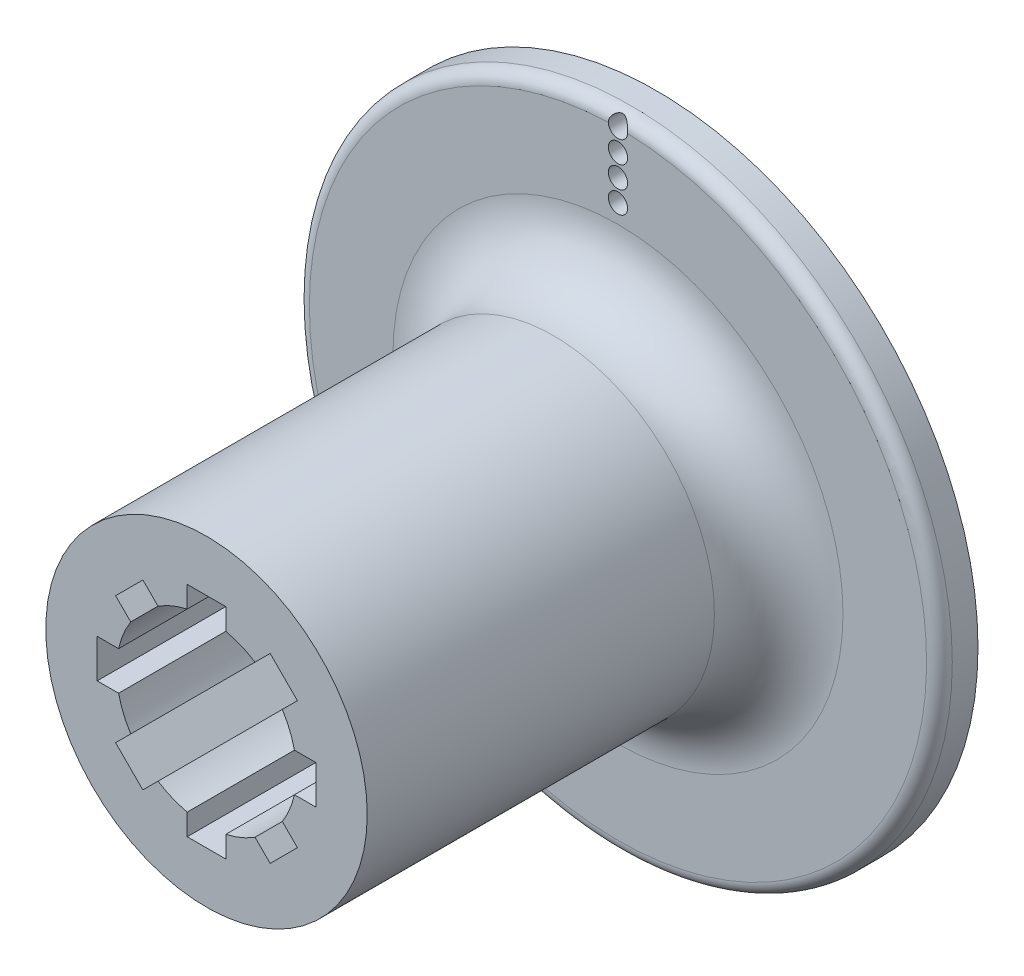
SolidWorks part; units mm, degrees
ref_plane "Front Plane" through (0, 0, 0) normal (0, 0, 1) x (1, 0, 0)
ref_plane "Top Plane" through (0, 0, 0) normal (0, 1, 0) x (1, 0, 0)
ref_plane "Right Plane" through (0, 0, 0) normal (1, 0, 0) x (0, 0, -1)
sketch "Sketch1" plane through (0, 0, 0) normal (0, 0, 1) x (1, 0, 0)
  circle A0 centre (0, 0) radius 28.1
  circle A1 centre (0, 28.1) radius 2.7
  circle A2 centre (24.3353, 14.05) radius 2.7
  circle A3 centre (24.3353, -14.05) radius 2.7
  circle A4 centre (0, -28.1) radius 2.7
  circle A5 centre (-24.3353, -14.05) radius 2.7
  circle A6 centre (-24.3353, 14.05) radius 2.7
  point P18 (0, 0)
  dimension "D1" = 56.2
  dimension "D2" = 5.4
  dimension "D3" = 6
sketch "Sketch3" plane through (0, 0, 0) normal (0, 0, 1) x (1, 0, 0)
  circle A0 centre (0, 0) radius 25
  dimension "D1" = 50
extrude "Boss-Extrude1" add sketch "Sketch3" against normal blind 70
sketch "Sketch4" plane through (0, 0, -70) normal (0, 0, -1) x (-1, 0, 0)
  line L0 (-2.55, 6.6263) -> (-2.55, 9.1)
  line L1 (-2.55, 9.1) -> (2.55, 9.1)
  line L2 (2.55, 9.1) -> (2.55, 6.6263)
  line L3 (0, 0) -> (0, 9.1) construction
  arc A0 (-2.55, 6.6263) -> (2.55, 6.6263) centre (0, 0) ccw
  dimension "D1" = 14.2
  dimension "D2" = 5.1
  dimension "D3" = 16.2
extrude "Cut-Extrude1" cut sketch "Sketch4" against normal blind 32
chamfer "Chamfer1" distance 1 angle 45 4 edges at (-2.55, 7.8631, -70) (0, 9.1, -70) (2.55, 7.8631, -70) (0, -7.1, -70)
sketch "Sketch7" plane through (0, 0, 0) normal (0, 0, 1) x (1, 0, 0)
  line L0 (0, 0) -> (0, 17) construction
  line L1 (-3, 17) -> (3, 17)
  line L2 (-3, 13.6748) -> (-3, 17)
  line L3 (3, 13.6748) -> (3, 17)
  line L4 (7.5482, 11.7909) -> (9.8995, 14.1421)
  line L5 (9.8995, 14.1421) -> (14.1421, 9.8995)
  line L6 (11.7909, 7.5482) -> (14.1421, 9.8995)
  line L7 (13.6748, 3) -> (17, 3)
  line L8 (17, 3) -> (17, -3)
  line L9 (13.6748, -3) -> (17, -3)
  line L10 (11.7909, -7.5482) -> (14.1421, -9.8995)
  line L11 (14.1421, -9.8995) -> (9.8995, -14.1421)
  line L12 (7.5482, -11.7909) -> (9.8995, -14.1421)
  line L13 (3, -13.6748) -> (3, -17)
  line L14 (3, -17) -> (-3, -17)
  line L15 (-3, -13.6748) -> (-3, -17)
  line L16 (-7.5482, -11.7909) -> (-9.8995, -14.1421)
  line L17 (-9.8995, -14.1421) -> (-14.1421, -9.8995)
  line L18 (-11.7909, -7.5482) -> (-14.1421, -9.8995)
  line L19 (-13.6748, -3) -> (-17, -3)
  line L20 (-17, -3) -> (-17, 3)
  line L21 (-13.6748, 3) -> (-17, 3)
  line L22 (-11.7909, 7.5482) -> (-14.1421, 9.8995)
  line L23 (-14.1421, 9.8995) -> (-9.8995, 14.1421)
  line L24 (-7.5482, 11.7909) -> (-9.8995, 14.1421)
  circle A0 centre (0, 0) radius 17 construction
  arc A1 (7.5482, 11.7909) -> (3, 13.6748) centre (0, 0) ccw
  circle A2 centre (0, 0) radius 25 construction
  arc A3 (-3, 13.6748) -> (-7.5482, 11.7909) centre (0, 0) ccw
  arc A4 (13.6748, 3) -> (11.7909, 7.5482) centre (0, 0) ccw
  arc A5 (11.7909, -7.5482) -> (13.6748, -3) centre (0, 0) ccw
  arc A6 (3, -13.6748) -> (7.5482, -11.7909) centre (0, 0) ccw
  arc A7 (-7.5482, -11.7909) -> (-3, -13.6748) centre (0, 0) ccw
  arc A8 (-13.6748, -3) -> (-11.7909, -7.5482) centre (0, 0) ccw
  arc A9 (-11.7909, 7.5482) -> (-13.6748, 3) centre (0, 0) ccw
  point P10 (0, 17)
  point P78 (0, 0)
  dimension "D1" = 8
  dimension "D2" = 3
  dimension "D3" = 6
  dimension "D4" = 8
extrude "Cut-Extrude4" cut sketch "Sketch7" against normal blind 30
sketch "Sketch15" plane through (0, 0, -30) normal (0, 0, 1) x (1, 0, 0)
  circle A0 centre (0, 0) radius 2.15
  dimension "D1" = 4.3
extrude "Cut-Extrude8" cut sketch "Sketch15" against normal through all
sketch "Sketch16" plane through (0, 0, -70) normal (0, 0, -1) x (-1, 0, 0)
  circle A0 centre (0, 0) radius 50
  circle A1 centre (0, 0) radius 25 construction
  circle A2 centre (0, 0) radius 25
  dimension "D1" = 100
extrude "Boss-Extrude2" add sketch "Sketch16" against normal blind 6
sketch "Sketch18" plane through (0, 0, 0) normal (1, 0, 0) x (0, 0, -1)
  line L0 (69.2, 50) -> (69.2, -50) construction
  line L1 (70, 50) -> (64, 50) construction
  line L2 (64, -50) -> (70, -50) construction
  line L3 (70, -50) -> (70, 50) construction
  circle A0 centre (69.2, 48.055) radius 1.445
  circle A4 centre (69.2, 44.665) radius 1.445
  circle A5 centre (69.2, 41.275) radius 1.445
  circle A6 centre (69.2, 37.885) radius 1.445
  dimension "D1" = 2.89
  dimension "D3" = 4
  dimension "D4" = 0.5
  dimension "D5" = 0.5
  dimension "D2" = 0.8
sketch "Sketch19" plane through (0, 0, -70) normal (0, 0, -1) x (-1, 0, 0)
  circle A0 centre (0, 0) radius 37.885
  circle A1 centre (0, 0) radius 41.275
  circle A2 centre (0, 0) radius 44.665
  circle A3 centre (0, 0) radius 48.055
sweep "Cut-Sweep1" cut profiles "Sketch18" path "Sketch19"
fillet "Fillet1" radius 10 1 edges at (-25, 0, -64)
fillet "Fillet2" radius 2 1 edges at (-50, 0, -64)
sketch "Sketch20" plane through (0, 0, -70) normal (0, 0, -1) x (-1, 0, 0)
  line L0 (0, 39.33) -> (0, 36.44) construction
  circle A0 centre (0, 48.055) radius 1.5
  circle A1 centre (0, 0) radius 48.055 construction
  circle A2 centre (0, 44.665) radius 1.5
  circle A3 centre (0, 0) radius 44.665 construction
  circle A4 centre (0, 41.275) radius 1.5
  circle A5 centre (0, 0) radius 41.275 construction
  circle A6 centre (0, 37.885) radius 1.5
  dimension "D1" = 3
extrude "Cut-Extrude9" cut sketch "Sketch20" against normal blind 10
